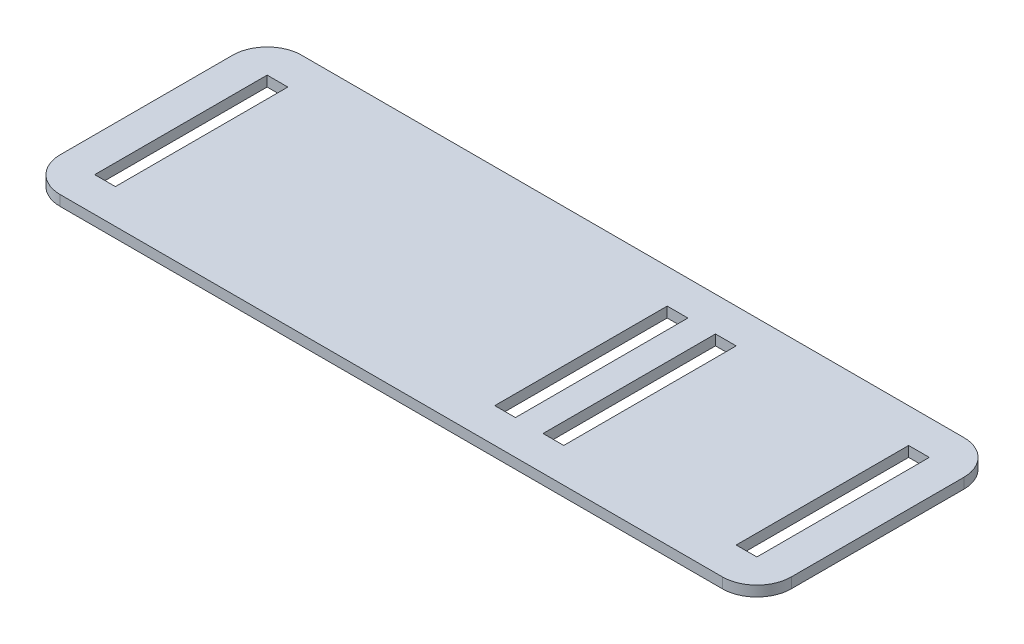
SolidWorks part; units mm, degrees
ref_plane "Front Plane" through (0, 0, 0) normal (0, 0, 1) x (1, 0, 0)
ref_plane "Top Plane" through (0, 0, 0) normal (0, 1, 0) x (1, 0, 0)
ref_plane "Right Plane" through (0, 0, 0) normal (1, 0, 0) x (0, 0, -1)
sketch "Sketch1" plane through (0, 0, 0) normal (0, 1, 0) x (1, 0, 0)
  line L1 (-106, -35) -> (106, -35)
  line L2 (-106, -35) -> (-106, 35)
  line L3 (-106, 35) -> (106, 35)
  line L4 (106, -35) -> (106, 35)
  line L5 (-106, -35) -> (106, 35) construction
  line L6 (-106, 35) -> (106, -35) construction
  point P0 (0, 0)
  dimension "D1" = 70
  dimension "D2" = 212
extrude "Boss-Extrude1" add sketch "Sketch1" along normal blind 3
sketch "Sketch2" plane through (0, 3, 0) normal (0, 1, 0) x (1, 0, 0)
  line L0 (20, -25) -> (26, -25)
  line L1 (-96, -25) -> (-90, -25)
  line L2 (-96, -25) -> (-96, 25)
  line L3 (-96, 25) -> (-90, 25)
  line L4 (-90, -25) -> (-90, 25)
  line L5 (-96, -25) -> (-90, 25) construction
  line L6 (-96, 25) -> (-90, -25) construction
  line L7 (20, -25) -> (20, 25)
  line L8 (20, 25) -> (26, 25)
  line L9 (26, -25) -> (26, 25)
  line L10 (34, -25) -> (40, -25)
  line L11 (34, -25) -> (34, 25)
  line L12 (34, 25) -> (40, 25)
  line L13 (40, -25) -> (40, 25)
  line L14 (90, -25) -> (96, -25)
  line L15 (90, -25) -> (90, 25)
  line L16 (90, 25) -> (96, 25)
  line L17 (96, -25) -> (96, 25)
  line L18 (-106, 35) -> (-106, -35) construction
  point P0 (-93, 0)
  point P5 (-26.7872, 0)
  point P6 (0, 0)
  dimension "D1" = 6
  dimension "D2" = 50
  dimension "D3" = 110
  dimension "D4" = 20
  dimension "D5" = 50
  dimension "D6" = 10
extrude "Cut-Extrude1" cut sketch "Sketch2" against normal through all both and the other way through all
fillet "Fillet1" radius 10 4 edges at (-106, 1.5, 35) (106, 1.5, 35) (106, 1.5, -35) (-106, 1.5, -35)
